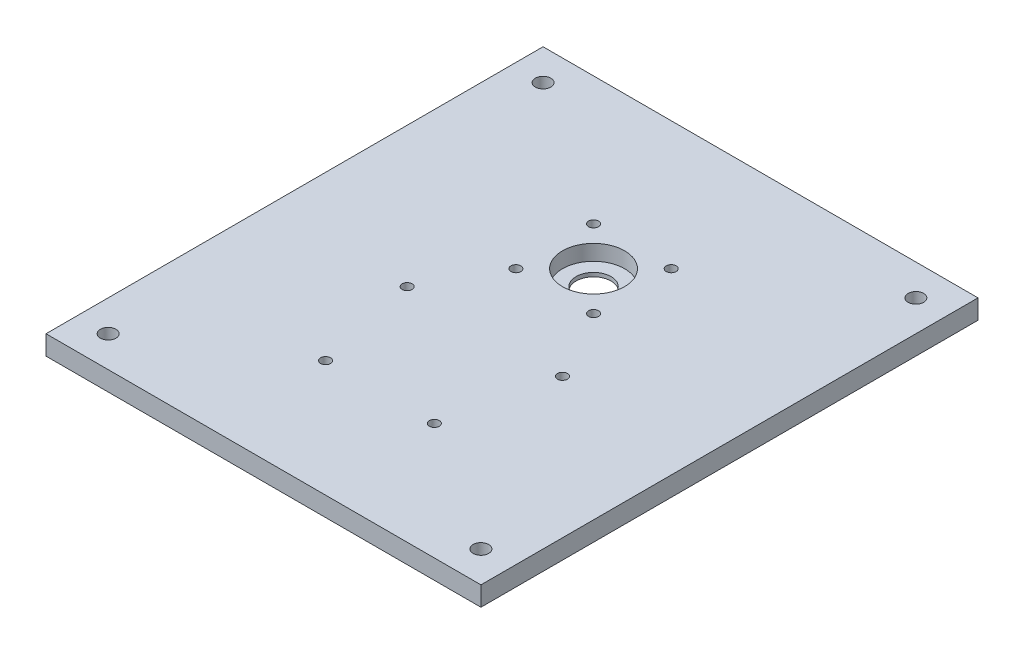
SolidWorks part; units mm, degrees
material "6061 Alloy"
ref_plane "Front Plane" through (0, 0, 0) normal (0, 0, 1) x (1, 0, 0)
ref_plane "Top Plane" through (0, 0, 0) normal (0, 1, 0) x (1, 0, 0)
ref_plane "Right Plane" through (0, 0, 0) normal (1, 0, 0) x (0, 0, -1)
sketch "Sketch1" plane through (0, 0, 0) normal (0, 1, 0) x (1, 0, 0)
  line L1 (-177.8, 203.2) -> (177.8, 203.2)
  line L2 (-177.8, 203.2) -> (-177.8, -203.2)
  line L3 (-177.8, -203.2) -> (177.8, -203.2)
  line L4 (177.8, 203.2) -> (177.8, -203.2)
  line L5 (-177.8, 203.2) -> (177.8, -203.2) construction
  line L6 (-177.8, -203.2) -> (177.8, 203.2) construction
  point P0 (0, 0)
  dimension "D1" = 406.4
  dimension "D2" = 355.6
extrude "Boss-Extrude1" add sketch "Sketch1" along normal blind 15.875
sketch "Sketch2" plane through (0, 15.875, 0) normal (0, 1, 0) x (1, 0, 0)
  line L0 (177.8, 203.2) -> (-177.8, 203.2) construction
  line L1 (-177.8, 203.2) -> (-177.8, -203.2) construction
  circle A0 centre (-152.4, 177.8) radius 6.35
  dimension "D2" = 12.7
  dimension "D1" = 25.4
  dimension "D3" = 25.4
extrude "Cut-Extrude1" cut sketch "Sketch2" against normal through all
ref_plane "Plane1" through (0, 0, 0) normal (-1, 0, 0) x (0, 0, 1)
ref_plane "Plane2" through (0, 0, 0) normal (0, 0, -1) x (-1, 0, 0)
mirror "Mirror1" about plane through (0, 0, 0) normal (-1, 0, 0) of "Cut-Extrude1"
mirror "Mirror2" about plane through (0, 0, 0) normal (0, 0, -1) of "Mirror1", "Cut-Extrude1"
sketch "Sketch3" plane through (0, 15.875, 0) normal (0, 1, 0) x (1, 0, 0)
  line L0 (0, 203.2) -> (0, -203.2) construction
  line L1 (177.8, 203.2) -> (-177.8, 203.2) construction
  line L2 (-177.8, -203.2) -> (177.8, -203.2) construction
  line L3 (0, 0) -> (177.8, 0) construction
  line L4 (-63.5, -22.225) -> (63.5, -22.225) construction
  line L6 (-44.45, -107.95) -> (44.45, -107.95) construction
  line L10 (177.8, -203.2) -> (177.8, 203.2) construction
  line L12 (-31.75, 98.425) -> (31.75, 98.425) construction
  line L13 (-31.75, 98.425) -> (-31.75, 34.925) construction
  line L14 (-31.75, 34.925) -> (31.75, 34.925) construction
  line L15 (31.75, 98.425) -> (31.75, 34.925) construction
  line L16 (-31.75, 98.425) -> (31.75, 34.925) construction
  line L17 (-31.75, 34.925) -> (31.75, 98.425) construction
  circle A0 centre (0, 66.675) radius 14.2875
  circle A2 centre (-63.5, -22.225) radius 4.064
  circle A3 centre (63.5, -22.225) radius 4.064
  circle A4 centre (44.45, -107.95) radius 4.064
  circle A5 centre (-44.45, -107.95) radius 4.064
  circle A6 centre (-31.75, 98.425) radius 4.064
  circle A7 centre (-31.75, 34.925) radius 4.064
  circle A8 centre (31.75, 98.425) radius 4.064
  circle A9 centre (31.75, 34.925) radius 4.064
  point P8 (0, -66.675)
  dimension "D1" = 28.575
  dimension "D4" = 41.275
  dimension "D5" = 8.128
  dimension "D7" = 8.128
  dimension "D2" = 63.5
  dimension "D3" = 133.35
  dimension "D6" = 88.9
  dimension "D8" = 127
  dimension "D9" = 44.45
extrude "Cut-Extrude2" cut sketch "Sketch3" against normal through all
sketch "Sketch4" plane through (0, 15.875, 0) normal (0, 1, 0) x (1, 0, 0)
  line L0 (14.2875, 66.675) -> (-14.2875, 66.675) construction
  circle A0 centre (0, 66.675) radius 14.2875 construction
  circle A1 centre (0, 66.675) radius 25.4
  dimension "D1" = 50.8
extrude "Cut-Extrude3" cut sketch "Sketch4" against normal blind 12.7
sketch "Sketch5" plane through (0, 0, 0) normal (0, -1, 0) x (1, 0, 0)
  circle A0 centre (-31.75, -98.425) radius 6.35
  circle A1 centre (31.75, -98.425) radius 6.35
  circle A2 centre (31.75, -34.925) radius 6.35
  circle A3 centre (-31.75, -34.925) radius 6.35
  circle A4 centre (-63.5, 22.225) radius 6.35
  circle A5 centre (63.5, 22.225) radius 6.35
  circle A6 centre (44.45, 107.95) radius 6.35
  circle A7 centre (-44.45, 107.95) radius 6.35
  dimension "D1" = 12.7
extrude "Cut-Extrude4" cut sketch "Sketch5" against normal blind 8.89
